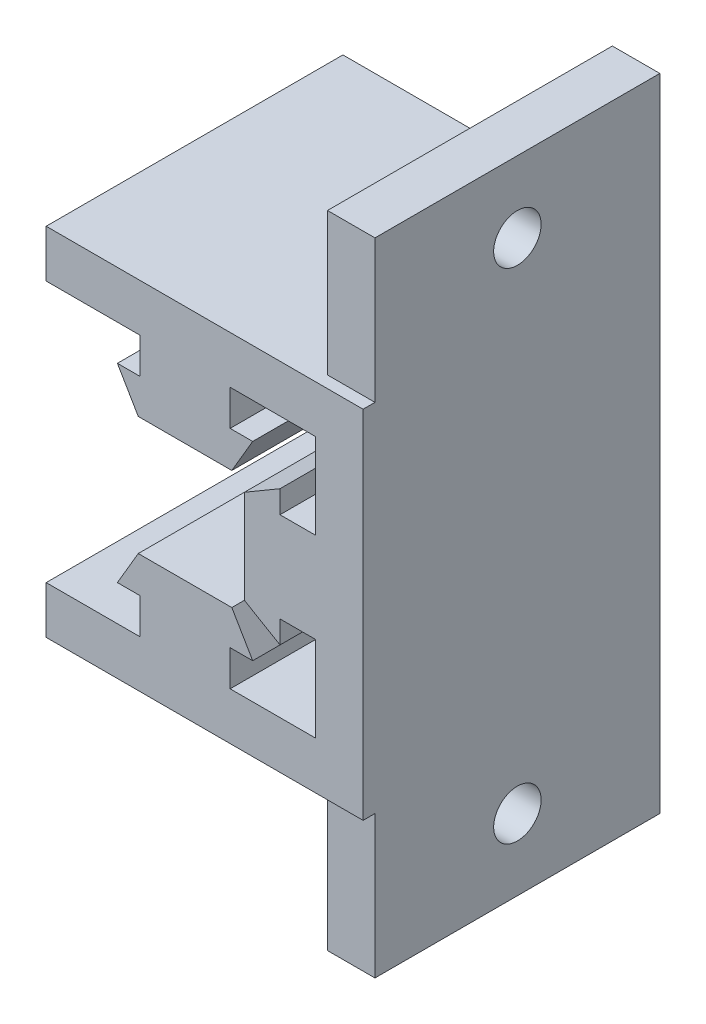
SolidWorks part; units mm, degrees
ref_plane "Plano frontal" through (0, 0, 0) normal (0, 0, 1) x (1, 0, 0)
ref_plane "Plano superior" through (0, 0, 0) normal (0, 1, 0) x (1, 0, 0)
ref_plane "Plano direito" through (0, 0, 0) normal (1, 0, 0) x (0, 0, -1)
sketch "Esboço1" plane through (0, 0, 0) normal (0, 0, 1) x (1, 0, 0)
  line L0 (-5.7, 33.5) -> (-3.9406, 30.5)
  line L1 (-3.8, 33.5) -> (-5.7, 33.5)
  line L2 (0, 30.5) -> (0, 33.5) construction
  line L3 (0, 33.5) -> (-3.8, 33.5) construction
  line L4 (-3.9406, 30.5) -> (3.9406, 30.5)
  line L5 (3.8, 33.5) -> (0, 33.5) construction
  line L6 (-5.508, 33.7422) -> (-5.7, 33.5)
  line L7 (5.7, 33.5) -> (5.8099, 33.2111)
  line L8 (3.8, 33.5) -> (3.8, 36.5)
  line L9 (3.9406, 30.5) -> (5.7, 33.5)
  line L10 (-3.8, 33.5) -> (-3.8, 36.5)
  line L11 (3.8, 33.5) -> (5.7, 33.5)
  line L12 (0, 30.5) -> (0, 26.3) construction
  line L13 (8, 31.2) -> (5, 29.4406)
  line L14 (8, 29.3) -> (8, 31.2)
  line L15 (5, 29.4406) -> (5, 21.5594)
  line L16 (8.2422, 31.008) -> (8, 31.2)
  line L17 (8, 19.8) -> (7.7111, 19.6901)
  line L18 (8, 21.7) -> (11, 21.7)
  line L19 (5, 21.5594) -> (8, 19.8)
  line L20 (8, 29.3) -> (11, 29.3)
  line L21 (8, 21.7) -> (8, 19.8)
  line L22 (11, 21.7) -> (11, 14.3)
  line L23 (15, 37.2) -> (15, 10.3)
  line L24 (-11.7, 14.5) -> (-11.7, 10.5)
  line L25 (11, 36.5) -> (11, 29.3)
  line L26 (5, 25.5) -> (8, 25.5) construction
  line L27 (8, 25.5) -> (8, 29.3) construction
  line L28 (8, 21.7) -> (8, 25.5) construction
  line L29 (5.7, 17.5) -> (3.9406, 20.5)
  line L30 (3.8, 17.5) -> (5.7, 17.5)
  line L31 (3.8, 36.5) -> (11.2, 36.5)
  line L32 (-11.7, 40.5) -> (15.2, 40.5)
  line L33 (-11.7, 40.5) -> (-11.7, 36.5)
  line L34 (-11.7, 36.5) -> (-3.8, 36.5)
  line L35 (3.9406, 20.5) -> (-3.9406, 20.5)
  line L36 (5.508, 17.2578) -> (5.7, 17.5)
  line L37 (-5.7, 17.5) -> (-5.8099, 17.7889)
  line L38 (-3.8, 17.5) -> (-3.8, 14.5)
  line L39 (-3.9406, 20.5) -> (-5.7, 17.5)
  line L40 (3.8, 17.5) -> (3.8, 14.5)
  line L41 (-3.8, 17.5) -> (-5.7, 17.5)
  line L42 (-3.8, 14.5) -> (-11.2, 14.5)
  line L43 (11.7, 10.5) -> (-11.7, 10.5)
  line L44 (-11.7, 10.5) -> (-11.7, 14.5)
  line L45 (11, 14.5) -> (3.8, 14.5)
  line L46 (0, 20.5) -> (0, 17.5) construction
  line L47 (0, 17.5) -> (3.8, 17.5) construction
  line L48 (-3.8, 17.5) -> (0, 17.5) construction
  line L49 (15, 37.2) -> (15, 40.5)
  line L50 (11.7, 10.5) -> (15, 10.5)
  line L51 (-3.8, 14.5) -> (-11.7, 14.5)
  line L91 (15, 37.2) -> (11, 37.2) [skipped]
  line L92 (11.7, 10.5) -> (11.7, 14.5) [skipped]
  point P52 (0, 25.5)
  dimension "D6" = 3
  dimension "D1" = 11.4
  dimension "D2" = 4.2
  dimension "D3" = 7.6
  dimension "D4" = 3
  dimension "D5" = 4
  dimension "D7" = 5.7
  dimension "D9" = 6
extrude "Ressalto-extrusão3" add sketch "Esboço1" along normal blind 25
sketch "Esboço6" plane through (0, 0, 0) normal (0, 0, 1) x (1, 0, 0)
  line L1 (11, 36.5) -> (15, 36.5)
  line L2 (11, 36.5) -> (11, 52.5)
  line L3 (11, 52.5) -> (15, 52.5)
  line L4 (15, 36.5) -> (15, 52.5)
  line L5 (11, 14.5) -> (15, 14.5)
  line L6 (11, 14.5) -> (11, -1.5)
  line L7 (11, -1.5) -> (15, -1.5)
  line L8 (15, 14.5) -> (15, -1.5)
  dimension "D1" = 12
  dimension "D2" = 12
extrude "Ressalto-extrusão6" add sketch "Esboço6" along normal blind 24
sketch "Esboço7" plane through (0, 0, 0) normal (1, 0, 0) x (0, 0, -1)
  line L0 (0, 46.5) -> (-24, 46.5) construction
  line L1 (0, 52.5) -> (0, 40.5) construction
  line L2 (-24, 52.5) -> (-24, 40.5) construction
  line L3 (0, 4.5) -> (-24, 4.5) construction
  line L4 (0, 10.5) -> (0, -1.5) construction
  line L5 (-24, 10.5) -> (-24, -1.5) construction
  line L6 (-12, -1.5) -> (-12, 52.5) construction
  line L7 (-24, -1.5) -> (0, -1.5) construction
  line L8 (-24, 52.5) -> (0, 52.5) construction
  circle A0 centre (-12, 46.5) radius 2
  circle A1 centre (-12, 4.5) radius 2
  dimension "D1" = 4
  dimension "D2" = 4
extrude "Corte-extrusão3" cut sketch "Esboço7" along normal blind 43
